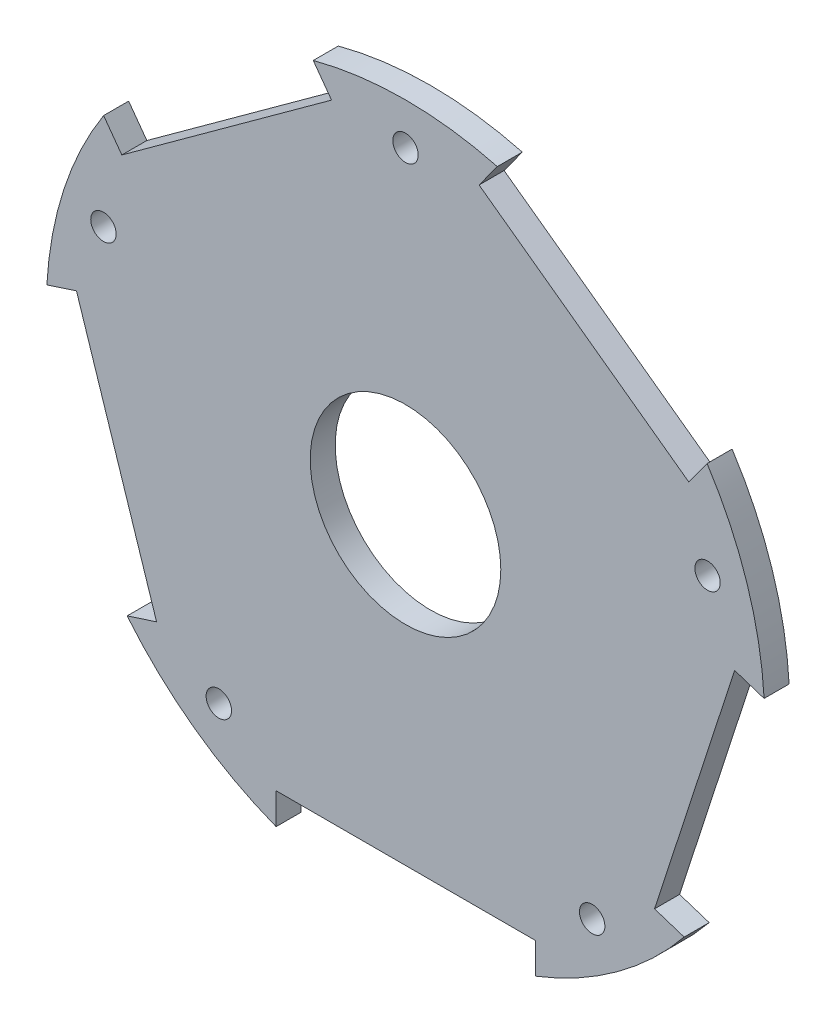
SolidWorks part; units mm, degrees
material "Pine"
ref_plane "Front Plane" through (0, 0, 0) normal (0, 0, 1) x (1, 0, 0)
ref_plane "Top Plane" through (0, 0, 0) normal (0, 1, 0) x (1, 0, 0)
ref_plane "Right Plane" through (0, 0, 0) normal (1, 0, 0) x (0, 0, -1)
sketch "Sketch1" plane through (0, 0, 0) normal (0, 0, 1) x (1, 0, 0)
  line L1 (165.3175, -85.5193) -> (168.9753, -80.4848)
  line L2 (93.9084, -116.0272) -> (90.2506, -110.9926)
  line L5 (207.2376, -115.976) -> (210.8953, -110.9415)
  line L6 (135.8284, -85.5705) -> (132.1706, -80.536)
  line L7 (216.3989, -144.006) -> (222.3173, -145.929)
  line L9 (200.3868, -193.286) -> (206.3053, -195.209)
  line L10 (176.5597, -210.6606) -> (176.5597, -216.8836)
  line L12 (124.7437, -210.6606) -> (124.7437, -216.8836)
  line L13 (100.8564, -193.3688) -> (94.938, -195.2918)
  line L15 (84.8444, -144.0888) -> (78.926, -146.0118)
  line L16 (165.3175, -85.5193) -> (207.2376, -115.976)
  line L17 (93.9084, -116.0272) -> (135.8284, -85.5705)
  line L18 (216.3989, -144.006) -> (200.3868, -193.286)
  line L19 (176.5597, -210.6606) -> (124.7437, -210.6606)
  line L20 (100.8564, -193.3688) -> (84.8444, -144.0888)
  arc A0 (90.2704, -111.0199) -> (78.926, -146.0118) centre (150.6082, -149.9164) ccw
  arc A1 (168.9555, -80.512) -> (132.1706, -80.536) centre (150.6082, -149.9164) ccw
  circle A3 centre (150.6082, -149.9164) radius 19.05
  arc A4 (222.2853, -145.9186) -> (210.8953, -110.9415) centre (150.6082, -149.9164) ccw
  arc A5 (176.5597, -216.8499) -> (206.3053, -195.209) centre (150.6082, -149.9164) ccw
  arc A6 (94.97, -195.2814) -> (124.7437, -216.8836) centre (150.6082, -149.9164) ccw
  point P0 (93.6844, -115.7189)
  point P8 (135.6044, -85.2622)
extrude "Boss-Extrude2" add sketch "Sketch1" along normal blind 5.0038
extrude "Cut-Extrude1" cut sketch "Sketch2" against normal blind 7.5438
sketch "Sketch2" plane through (0, 0, 0) normal (0, 0, -1) x (-1, 0, 0)
  circle A3 centre (-150.6084, -86.4355) radius 2.54
pattern_circular "CirPattern1" count 5 over 360 about axis through (150.6082, -149.9164, 0) along (0, 0, 1) of "Cut-Extrude1"
